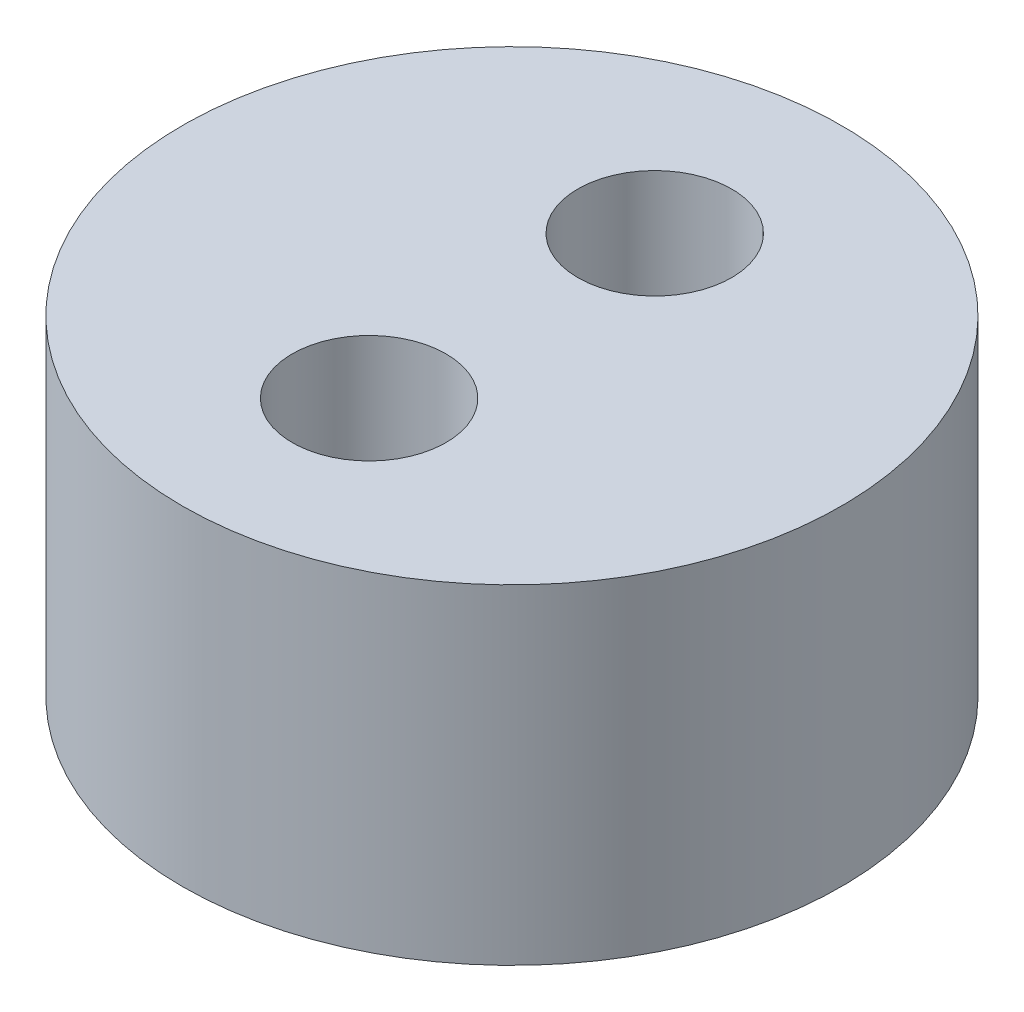
SolidWorks part; units mm, degrees
ref_plane "前视基准面" through (0, 0, 0) normal (0, 0, 1) x (1, 0, 0)
ref_plane "上视基准面" through (0, 0, 0) normal (0, 1, 0) x (1, 0, 0)
ref_plane "右视基准面" through (0, 0, 0) normal (1, 0, 0) x (0, 0, -1)
sketch "草图1" plane through (0, 0, 0) normal (0, 1, 0) x (1, 0, 0)
  circle A0 centre (0, 0) radius 3
extrude "凸台-拉伸1" add sketch "草图1" along normal blind 3
sketch "草图2" plane through (0, 3, 0) normal (0, 1, 0) x (1, 0, 0)
  circle A0 centre (0, 1.3) radius 0.7
  circle A1 centre (0, -1.3) radius 0.7
  point P0 (0, 0)
extrude "切除-拉伸1" cut sketch "草图2" against normal blind 3
